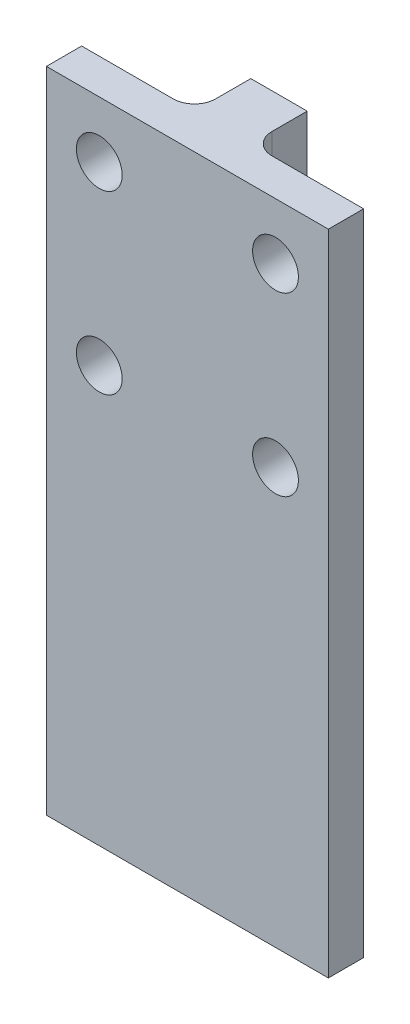
SolidWorks part; units mm, degrees
ref_plane "Front Plane" through (0, 0, 0) normal (0, 0, 1) x (1, 0, 0)
ref_plane "Top Plane" through (0, 0, 0) normal (0, 1, 0) x (1, 0, 0)
ref_plane "Right Plane" through (0, 0, 0) normal (1, 0, 0) x (0, 0, -1)
sketch "Sketch1" plane through (0, 0, 0) normal (0, 1, 0) x (1, 0, 0)
  line L0 (0, 0) -> (0, 13) construction
  line L5 (-4, 5) -> (-4, 13)
  line L6 (-20, 0) -> (20, 0)
  line L8 (4, 5) -> (20, 5)
  line L9 (20, 0) -> (20, 5)
  line L12 (-4, 13) -> (4, 13)
  line L13 (4, 5) -> (4, 13)
  line L14 (-20, 0) -> (-20, 5)
  line L15 (-4, 5) -> (-20, 5)
  point P10 (0, 13)
  dimension "D1" = 40
  dimension "D2" = 5
  dimension "D3" = 8
  dimension "D4" = 8
extrude "Boss-Extrude1" add sketch "Sketch1" against normal blind 92 contours L15 L14 L6 L9 L8 L13 L12 L5
fillet "Fillet1" radius 3 2 edges at (4, -46, -5) (-4, -46, -5)
sketch "Sketch2" plane through (0, 0, 0) normal (0, 0, 1) x (1, 0, 0)
  line L0 (0, 0) -> (0, -8) construction
  line L1 (0, -8) -> (12.5, -8) construction
  line L2 (0, -8) -> (0, -33) construction
  line L3 (0, -33) -> (12.5, -33) construction
  circle A0 centre (12.5, -8) radius 3.25
  circle A1 centre (12.5, -33) radius 3.25
  circle A2 centre (-12.5, -33) radius 3.25
  circle A3 centre (-12.5, -8) radius 3.25
  dimension "D3" = 6.5
  dimension "D1" = 8
  dimension "D2" = 12.5
  dimension "D4" = 25
extrude "Cut-Extrude1" cut sketch "Sketch2" against normal blind 92
